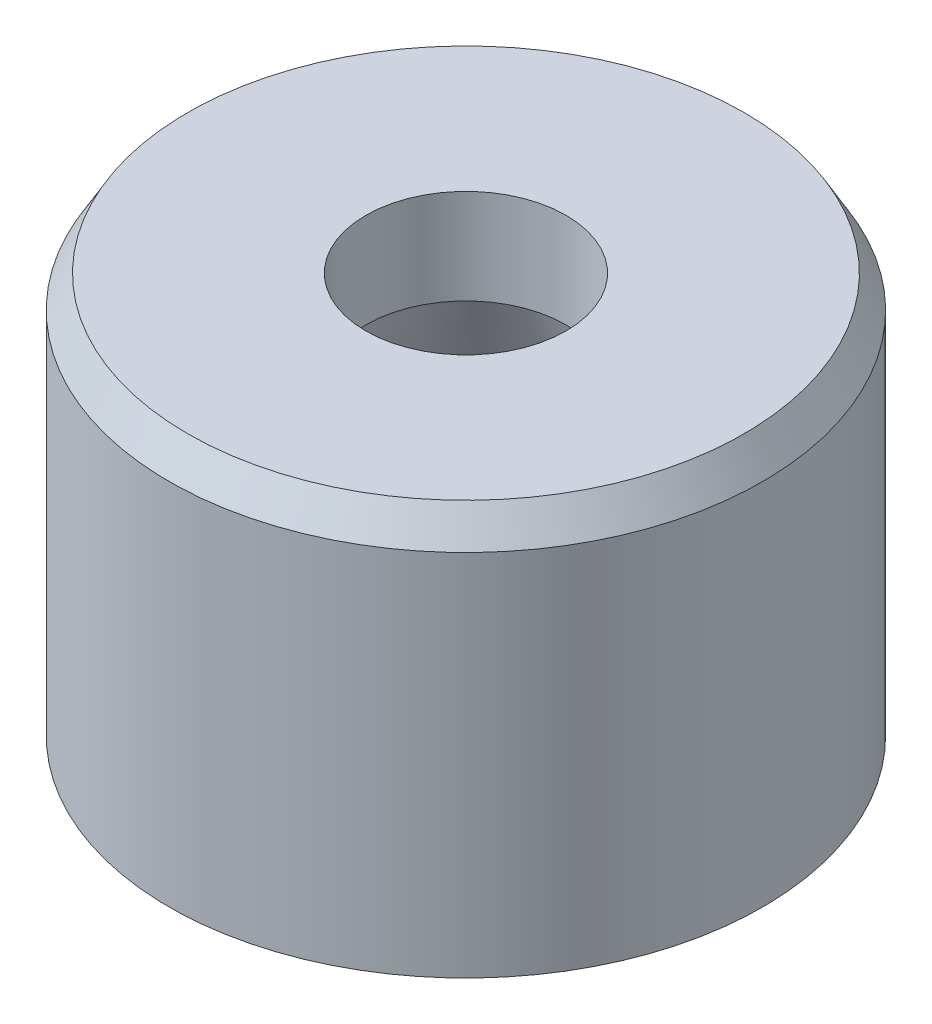
SolidWorks part; units mm, degrees
ref_plane "Front Plane" through (0, 0, 0) normal (0, 0, 1) x (1, 0, 0)
ref_plane "Top Plane" through (0, 0, 0) normal (0, 1, 0) x (1, 0, 0)
ref_plane "Right Plane" through (0, 0, 0) normal (1, 0, 0) x (0, 0, -1)
sketch "Sketch1" plane through (0, 0, 0) normal (0, 0, 1) x (1, 0, 0)
  line L0 (7.5, 10.8) -> (2.7, 10.8)
  line L1 (2.7, 10.8) -> (2.7, 8.2424)
  line L2 (2.7, 8.2424) -> (5.7, 0)
  line L3 (5.7, 0) -> (8, 0)
  line L4 (8, 0) -> (8, 9.934)
  line L5 (8, 9.934) -> (7.5, 10.8)
  line L6 (0, 10.8) -> (0, 0) construction
revolve "Revolve1" add sketch "Sketch1" angle 360 about L6
